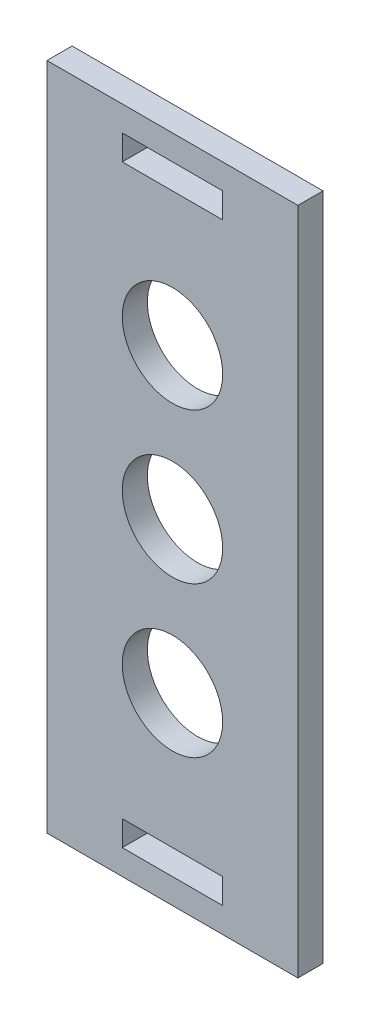
SolidWorks part; units mm, degrees
ref_plane "前视基准面" through (0, 0, 0) normal (0, 0, 1) x (1, 0, 0)
ref_plane "上视基准面" through (0, 0, 0) normal (0, 1, 0) x (1, 0, 0)
ref_plane "右视基准面" through (0, 0, 0) normal (1, 0, 0) x (0, 0, -1)
sketch "草图1" plane through (0, 0, 0) normal (0, 0, 1) x (1, 0, 0)
  line L0 (615.694, 391.4199) -> (615.694, 311.4199)
  line L1 (645.694, 391.4199) -> (645.694, 311.4199)
  line L2 (624.694, 317.4199) -> (636.694, 317.4199)
  line L3 (624.694, 314.4199) -> (636.694, 314.4199)
  line L4 (615.694, 311.4199) -> (645.694, 311.4199)
  line L5 (624.694, 385.4199) -> (636.694, 385.4199)
  line L6 (624.694, 388.4199) -> (636.694, 388.4199)
  line L7 (615.694, 391.4199) -> (645.694, 391.4199)
  line L8 (624.694, 388.4199) -> (624.694, 385.4199)
  line L9 (624.694, 317.4199) -> (624.694, 314.4199)
  line L10 (636.694, 388.4199) -> (636.694, 385.4199)
  line L11 (636.694, 317.4199) -> (636.694, 314.4199)
  circle A0 centre (630.694, 351.4199) radius 6
  circle A1 centre (630.694, 369.4199) radius 6
  circle A2 centre (630.694, 333.4199) radius 6
extrude "凸台-拉伸1" add sketch "草图1" along normal blind 3
